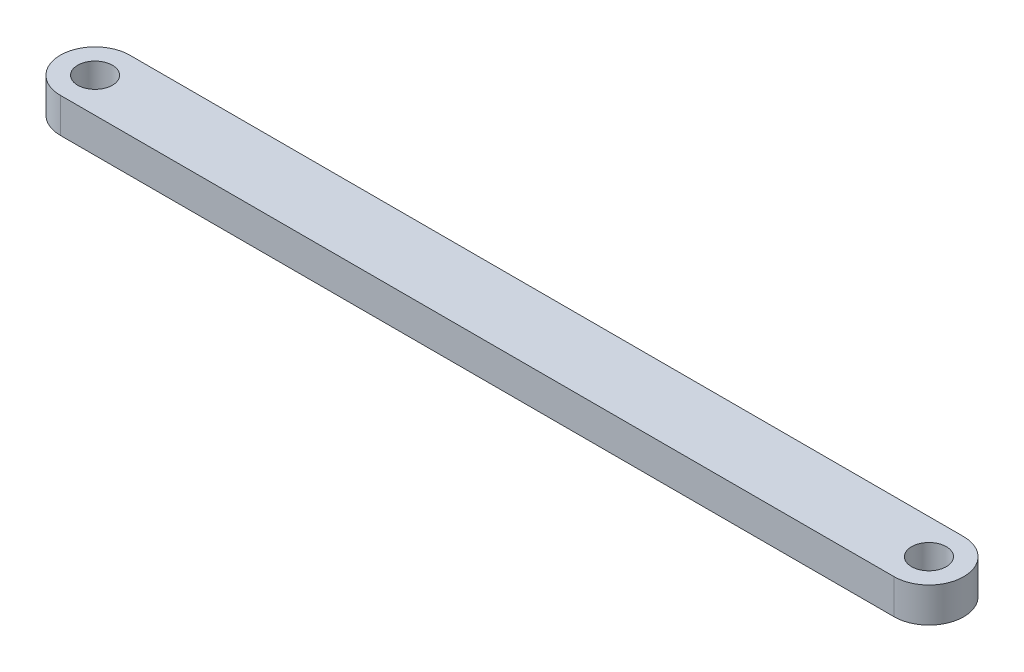
SolidWorks part; units mm, degrees
ref_plane "Front Plane" through (0, 0, 0) normal (0, 0, 1) x (1, 0, 0)
ref_plane "Top Plane" through (0, 0, 0) normal (0, 1, 0) x (1, 0, 0)
ref_plane "Right Plane" through (0, 0, 0) normal (1, 0, 0) x (0, 0, -1)
sketch "Sketch2" plane through (0, 0, 0) normal (0, 1, 0) x (1, 0, 0)
  line L0 (60, 0) -> (-60, 0) construction
  line L1 (60, -5) -> (-60, -5)
  line L2 (60, 5) -> (-60, 5)
  arc A0 (60, -5) -> (60, 5) centre (60, 0) ccw
  arc A1 (-60, 5) -> (-60, -5) centre (-60, 0) ccw
  circle A2 centre (60, 0) radius 2.5
  circle A3 centre (-60, 0) radius 2.5
  point P3 (0, 0)
  dimension "D2" = 5
  dimension "D3" = 5
  dimension "D1" = 120
extrude "Boss-Extrude1" add sketch "Sketch2" along normal blind 5
